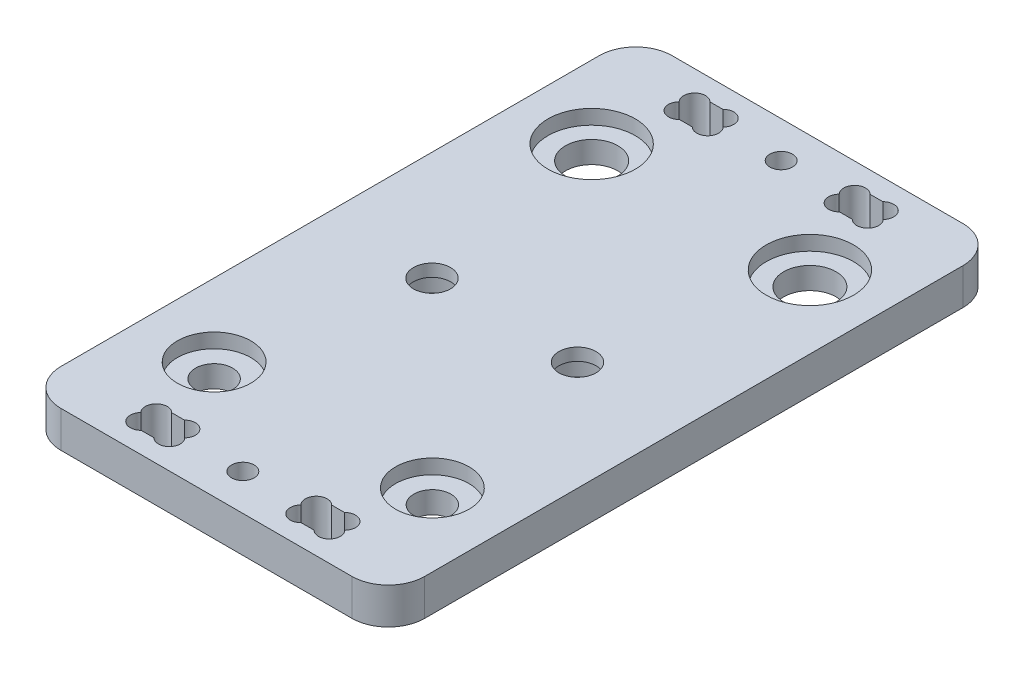
SolidWorks part; units mm, degrees
material "6061-T6 (SS)"
ref_plane "Front Plane" through (0, 0, 0) normal (0, 0, 1) x (1, 0, 0)
ref_plane "Top Plane" through (0, 0, 0) normal (0, 1, 0) x (1, 0, 0)
ref_plane "Right Plane" through (0, 0, 0) normal (1, 0, 0) x (0, 0, -1)
sketch "Sketch1" plane through (0, 0, 0) normal (0, 1, 0) x (1, 0, 0)
  line L0 (-23.7657, 0) -> (0, 0) construction
  line L1 (20.365, -35) -> (-20.365, -35)
  line L2 (25, -30.365) -> (25, 30.365)
  line L3 (20.365, 35) -> (-20.365, 35)
  line L4 (-25, -30.365) -> (-25, 30.365)
  line L5 (25, -35) -> (-25, 35) construction
  line L6 (25, 35) -> (-25, -35) construction
  line L7 (0, 0) -> (0, 28.9978) construction
  arc A0 (-20.365, 35) -> (-25, 30.365) centre (-20.365, 30.365) ccw
  arc A1 (25, 30.365) -> (20.365, 35) centre (20.365, 30.365) ccw
  arc A2 (-20.365, -35) -> (-25, -30.365) centre (-20.365, -30.365) cw
  arc A3 (20.365, -35) -> (25, -30.365) centre (20.365, -30.365) ccw
  circle A4 centre (-15, 25.95) radius 3.6
  circle A16 centre (15, 25.95) radius 3.6
  circle A33 centre (15, -25.95) radius 2.55
  circle A34 centre (-15, -25.95) radius 2.55
  point P0 (0, 0)
  dimension "D2" = 4.635
  dimension "D3" = 30
  dimension "D4" = 7.2
  dimension "D5" = 5.1
  dimension "D6" = 70
  dimension "D7" = 50
  dimension "D10" = 51.9
extrude "Boss-Extrude1" add sketch "Sketch1" along normal blind 5
sketch "Sketch2" plane through (0, 5, 0) normal (0, 1, 0) x (1, 0, 0)
  circle A0 centre (-15, 25.95) radius 6
  circle A1 centre (15, 25.95) radius 6
  circle A2 centre (15, -25.95) radius 5.05
  circle A3 centre (-15, -25.95) radius 5.05
  dimension "D1" = 12
  dimension "D2" = 10.1
extrude "Cut-Extrude1" cut sketch "Sketch2" against normal blind 2
sketch "Croquis3" plane through (0, 5, 0) normal (0, 1, 0) x (1, 0, 0)
  line L0 (-25, 30.365) -> (-25, -30.365) construction
  line L1 (25, -30.365) -> (25, 30.365) construction
  line L2 (-20.365, -35) -> (20.365, -35) construction
  line L3 (0, 0) -> (38.7816, 0) construction
  line L4 (-25, 30.365) -> (-25, 37)
  line L5 (-20, 42) -> (20, 42)
  line L6 (25, 37) -> (25, 30.365)
  line L7 (-20.365, 35) -> (20.365, 35)
  line L8 (-20.365, -35) -> (20.365, -35)
  line L9 (25, -37) -> (25, -30.365)
  line L10 (-20, -42) -> (20, -42)
  line L11 (-25, -30.365) -> (-25, -37)
  arc A0 (-25, -30.365) -> (-20.365, -35) centre (-20.365, -30.365) ccw construction
  arc A1 (20.365, -35) -> (25, -30.365) centre (20.365, -30.365) ccw construction
  arc A2 (25, 30.365) -> (20.365, 35) centre (20.365, 30.365) ccw
  arc A3 (-20.365, 35) -> (-25, 30.365) centre (-20.365, 30.365) ccw
  arc A4 (-25, -37) -> (-20, -42) centre (-20, -37) ccw
  arc A5 (20, -42) -> (25, -37) centre (20, -37) ccw
  arc A6 (-20.365, -35) -> (-25, -30.365) centre (-20.365, -30.365) cw
  arc A7 (25, -30.365) -> (20.365, -35) centre (20.365, -30.365) cw
  arc A8 (20, 42) -> (25, 37) centre (20, 37) cw
  arc A9 (-25, 37) -> (-20, 42) centre (-20, 37) cw
  dimension "D2" = 5
  dimension "D1" = 7
extrude "Saliente-Extruir1" add sketch "Croquis3" against normal up to surface (5 mm away) up to face at (0, 0, 0)
sketch "Croquis5" plane through (0, 0, 0) normal (0, -1, 0) x (1, 0, 0)
  line L0 (-10, 1) -> (10, 1) construction
  line L1 (0, 1) -> (0, 0) construction
  circle A0 centre (10, 1) radius 2.55
  circle A1 centre (-10, 1) radius 2.55
  dimension "D1" = 5.1
  dimension "D2" = 20
  dimension "D3" = 1
extrude "Cortar-Extruir2" cut sketch "Croquis5" against normal through all
sketch "Croquis6" plane through (0, 5, 0) normal (0, 1, 0) x (1, 0, 0)
  line L0 (-30.2461, -34.9) -> (-14, -34.9) construction
  line L1 (-25, -37) -> (-11, -37) construction
  line L2 (-20, -42) -> (20, -42) construction
  line L3 (0, -39.1) -> (0, -34.9) construction
  line L4 (25, -37) -> (11, -37) construction
  line L5 (-25, -39.1) -> (-14, -39.1) construction
  line L6 (-25, -39.1) -> (-25, -34.9) construction
  line L7 (-25, 37) -> (-25, -37) construction
  line L8 (25, -39.1) -> (25, -34.9) construction
  line L9 (25, -37) -> (25, 37) construction
  line L10 (-14, -39.1) -> (-8, -39.1) construction
  line L12 (-8, -34.9) -> (-14, -34.9)
  line L14 (-8, -34.9) -> (29.3675, -34.9) construction
  line L15 (-8, -34.9) -> (-8, -39.1)
  line L16 (-8, -39.1) -> (-14, -39.1)
  line L17 (8, -34.9) -> (14, -34.9)
  line L18 (8, -34.9) -> (8, -39.1)
  line L19 (8, -39.1) -> (14, -39.1)
  line L20 (14, -34.9) -> (14, -39.1)
  line L21 (8, -34.9) -> (14, -39.1) construction
  line L22 (8, -39.1) -> (14, -34.9) construction
  line L27 (-8, -39.1) -> (25, -39.1) construction
  line L29 (-14, -34.9) -> (-14, -39.1)
  line L30 (-8, -34.9) -> (-14, -39.1) construction
  line L31 (-8, -39.1) -> (-14, -34.9) construction
  circle A0 centre (0, -37) radius 1.55
  point P20 (-11, -37)
  point P25 (11, -37)
  dimension "D2" = 3.1
  dimension "D12" = 6
  dimension "D3" = 2.9
  dimension "D5" = 6
  dimension "D6" = 14
  dimension "D13" = 4.2
extrude "Cortar-Extruir3" cut sketch "Croquis6" against normal through all
sketch "Croquis7" plane through (0, 0, 0) normal (0, -1, 0) x (1, 0, 0)
  line L0 (-12.9393, 38.0393) -> (-9.0607, 38.0393) construction
  line L1 (-9.0607, 38.0393) -> (-9.0607, 35.9607) construction
  line L2 (-9.0607, 35.9607) -> (-12.9393, 35.9607) construction
  line L3 (-12.9393, 35.9607) -> (-12.9393, 38.0393) construction
  line L4 (-14, 34.9) -> (-14, 39.1) construction
  line L5 (-14, 39.1) -> (-8, 39.1) construction
  line L6 (-14, 39.1) -> (-12.5, 37.6) construction
  line L7 (-11.8787, 39.1) -> (-10.1213, 39.1)
  line L8 (-11.8787, 34.9) -> (-10.1213, 34.9)
  line L9 (-8, 34.9) -> (-14, 34.9) construction
  line L10 (0, 37) -> (0, 28.6327) construction
  line L11 (11.8787, 34.9) -> (10.1213, 34.9)
  line L12 (11.8787, 39.1) -> (10.1213, 39.1)
  arc A0 (-11.8787, 39.1) -> (-14.0209, 37) centre (-12.9393, 38.0393) ccw
  arc A1 (-7.9791, 37) -> (-10.1213, 39.1) centre (-9.0607, 38.0393) ccw
  arc A2 (-10.1213, 34.9) -> (-7.9791, 37) centre (-9.0607, 35.9607) ccw
  arc A3 (-14.0209, 37) -> (-11.8787, 34.9) centre (-12.9393, 35.9607) ccw
  circle A4 centre (-12.5, 37.6) radius 1.5 construction
  arc A5 (14.0209, 37) -> (11.8787, 34.9) centre (12.9393, 35.9607) cw
  arc A6 (10.1213, 34.9) -> (7.9791, 37) centre (9.0607, 35.9607) cw
  arc A7 (7.9791, 37) -> (10.1213, 39.1) centre (9.0607, 38.0393) cw
  arc A8 (11.8787, 39.1) -> (14.0209, 37) centre (12.9393, 38.0393) cw
  dimension "D1" = 3
extrude "Cortar-Extruir4" cut sketch "Croquis7" against normal through all
sketch "Croquis8" plane through (0, 0, 0) normal (0, -1, 0) x (1, 0, 0)
  circle A0 centre (-10, 1) radius 4.625
  circle A1 centre (10, 1) radius 4.625
  dimension "D1" = 9.25
extrude "Cortar-Extruir5" cut sketch "Croquis8" against normal blind 3.3
sketch "Croquis9" plane through (0, 5, 0) normal (0, 1, 0) x (1, 0, 0)
  line L0 (-25, 37) -> (-25, -37) construction
  line L1 (-20, -42) -> (20, -42) construction
  circle A0 centre (-21, -11.48) radius 2.575
  dimension "D3" = 5.15
  dimension "D1" = 4
  dimension "D2" = 30.52
extrude "Cortar-Extruir6" [suppressed] cut sketch "Croquis9" against normal through all
mirror "Simetría1" about plane through (0, 0, 0) normal (0, 0, 1) of "Cortar-Extruir3", "Cortar-Extruir4"
